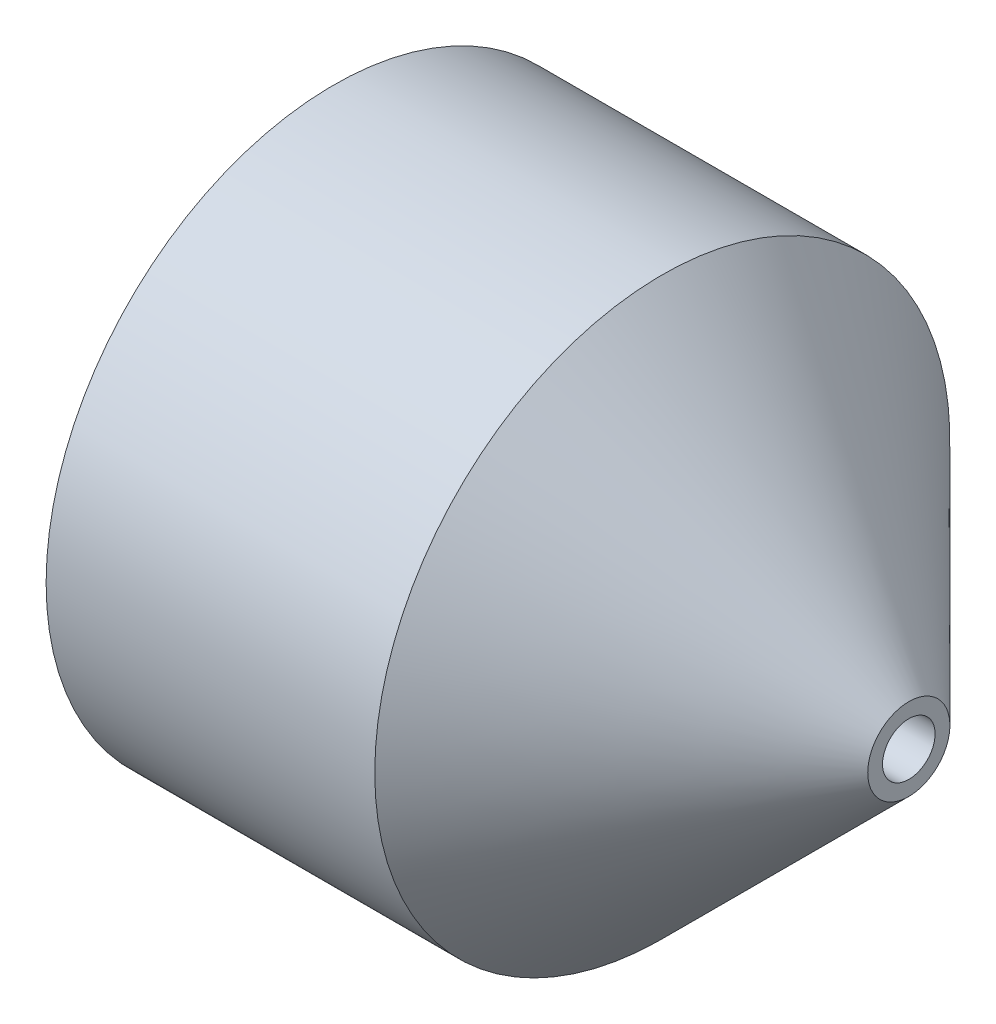
SolidWorks part; units mm, degrees
ref_plane "Front" through (0, 0, 0) normal (0, 0, 1) x (1, 0, 0)
ref_plane "Top" through (0, 0, 0) normal (0, 1, 0) x (1, 0, 0)
ref_plane "Right" through (0, 0, 0) normal (1, 0, 0) x (0, 0, -1)
sketch "Sketch1" plane through (0, 0, 0) normal (0, 0, 1) x (1, 0, 0)
  line L0 (-79.434, 0) -> (79.434, 0) construction
  line L1 (35, 1.6) -> (35, 2.5)
  line L2 (35, 1.6) -> (23, 1.6)
  line L3 (23, 1.6) -> (12.85, 11.75)
  line L4 (12.85, 11.75) -> (0, 11.75)
  line L5 (0, 11.75) -> (0, 17.5)
  line L6 (0, 17.5) -> (20, 17.5)
  line L7 (35, 2.5) -> (20, 17.5)
  dimension "D1" = 3.2
  dimension "D2" = 5
  dimension "D3" = 12
  dimension "D4" = 45
  dimension "D5" = 23.5
  dimension "D6" = 35
  dimension "D7" = 45
  dimension "D8" = 35
revolve "Revolve1" add sketch "Sketch1" angle 360 about L0
sketch "Sketch9" plane through (0, 0, 0) normal (-1, 0, 0) x (0, 0, 1)
  line L0 (0, 0) -> (0, 17.5)
  line L1 (0, 0) -> (17.5, 0)
  circle A0 centre (0, 0) radius 17.5 construction
